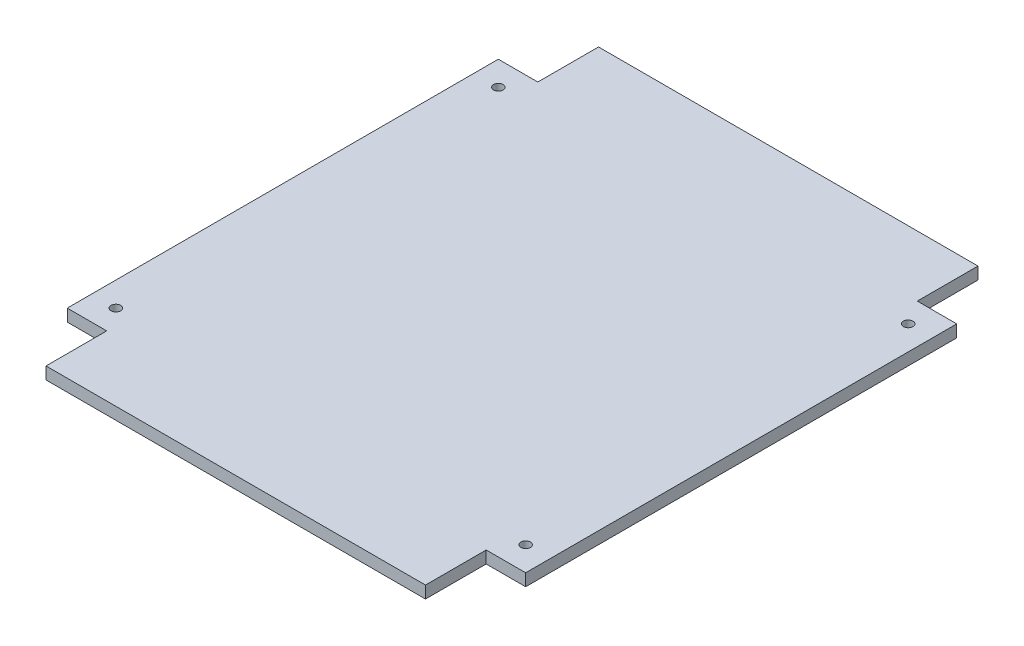
SolidWorks part; units mm, degrees
material "Copper"
ref_plane "Front Plane" through (0, 0, 0) normal (0, 0, 1) x (1, 0, 0)
ref_plane "Top Plane" through (0, 0, 0) normal (0, 1, 0) x (1, 0, 0)
ref_plane "Right Plane" through (0, 0, 0) normal (1, 0, 0) x (0, 0, -1)
sketch "Sketch1" plane through (0, 0, 0) normal (0, 1, 0) x (1, 0, 0)
  line L0 (-47.9425, 45.085) -> (-39.6875, 45.085)
  line L1 (39.6875, -57.785) -> (-39.6875, -57.785)
  line L2 (47.9425, -45.085) -> (47.9425, 45.085)
  line L3 (39.6875, 57.785) -> (-39.6875, 57.785)
  line L4 (-47.9425, -45.085) -> (-47.9425, 45.085)
  line L5 (47.9425, -57.785) -> (-47.9425, 57.785) construction
  line L6 (47.9425, 57.785) -> (-47.9425, -57.785) construction
  line L7 (-39.6875, 45.085) -> (-39.6875, 57.785)
  line L8 (0, 0) -> (0, 88.612) construction
  line L9 (47.9425, 45.085) -> (39.6875, 45.085)
  line L10 (39.6875, 45.085) -> (39.6875, 57.785)
  line L11 (0, 0) -> (102.5577, 0) construction
  line L12 (39.6875, -45.085) -> (39.6875, -57.785)
  line L13 (47.9425, -45.085) -> (39.6875, -45.085)
  line L14 (-47.9425, -45.085) -> (-39.6875, -45.085)
  line L15 (-39.6875, -45.085) -> (-39.6875, -57.785)
  point P0 (0, 0)
  dimension "D1" = 115.57
  dimension "D2" = 95.885
  dimension "D3" = 8.255
  dimension "D4" = 12.7
extrude "Boss-Extrude1" add sketch "Sketch1" along normal blind 2.54
sketch "Sketch5" plane through (0, 2.54, 0) normal (0, 1, 0) x (1, 0, 0)
  line L0 (-39.6875, -57.785) -> (39.6875, -57.785) construction
  line L1 (47.9425, -45.085) -> (47.9425, 45.085) construction
  circle A0 centre (42.8625, -40.005) radius 0.9995
  circle A1 centre (42.8625, 40.005) radius 0.9995
  circle A2 centre (-42.8625, -40.005) radius 0.9995
  circle A3 centre (-42.8625, 40.005) radius 0.9995
  dimension "D3" = 1.999
  dimension "D6" = 1.999
  dimension "D7" = 1.999
  dimension "D8" = 1.999
  dimension "D1" = 17.78
  dimension "D2" = 5.08
  dimension "D4" = 97.79
  dimension "D5" = 90.805
extrude "Cut-Extrude2" cut sketch "Sketch5" against normal through all
equation "\"Mounting Holes\"= .0787"
equation "\"D3@Sketch5\" = \"Mounting Holes\""
equation "\"D6@Sketch5\"=\"Mounting Holes\""
equation "\"D7@Sketch5\"=\"Mounting Holes\""
equation "\"D8@Sketch5\"=\"Mounting Holes\""
